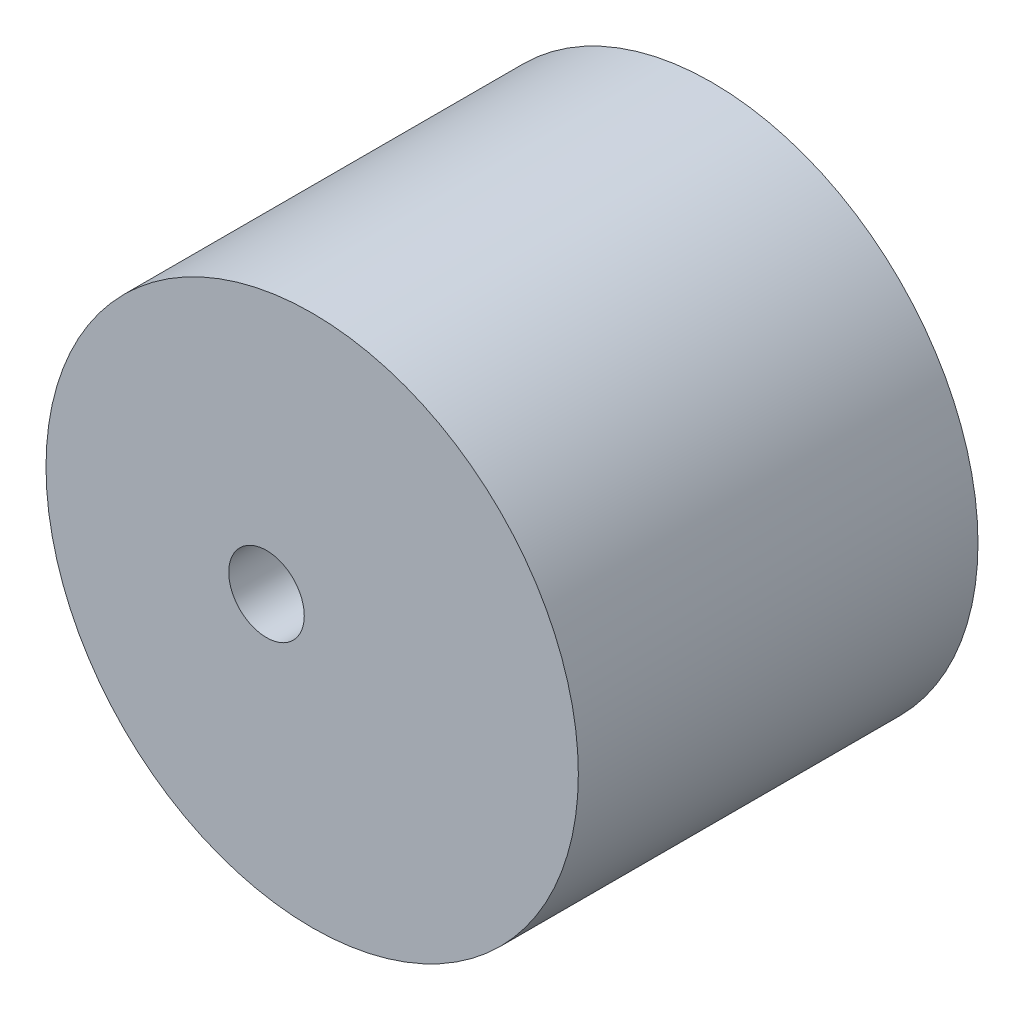
SolidWorks part; units mm, degrees
ref_plane "Front Plane" through (0, 0, 0) normal (0, 0, 1) x (1, 0, 0)
ref_plane "Top Plane" through (0, 0, 0) normal (0, 1, 0) x (1, 0, 0)
ref_plane "Right Plane" through (0, 0, 0) normal (1, 0, 0) x (0, 0, -1)
sketch "Sketch11" plane through (0, 0, 0) normal (0, 0, 1) x (1, 0, 0)
  circle A0 centre (0, 0) radius 23.3106
  circle A1 centre (-4, 0) radius 3.3085
extrude "Boss-Extrude13" add sketch "Sketch11" along normal blind 35
